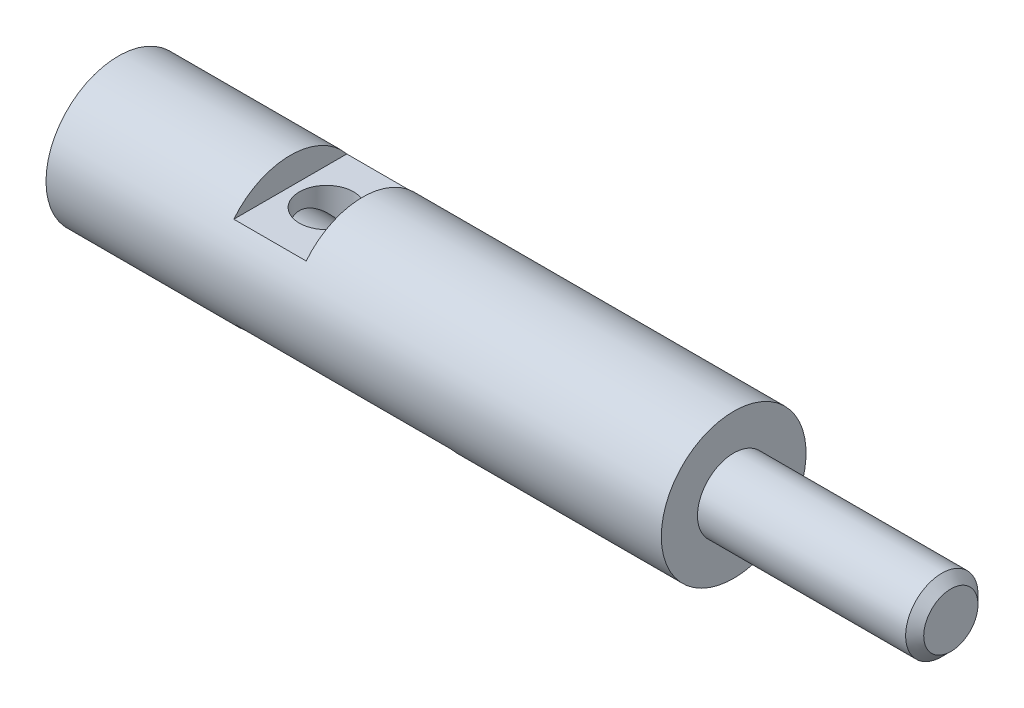
SolidWorks part; units mm, degrees
ref_plane "Front Plane" through (0, 0, 0) normal (0, 0, 1) x (1, 0, 0)
ref_plane "Top Plane" through (0, 0, 0) normal (0, 1, 0) x (1, 0, 0)
ref_plane "Right Plane" through (0, 0, 0) normal (1, 0, 0) x (0, 0, -1)
sketch "Эскиз1" plane through (0, 0, 0) normal (0, 0, 1) x (1, 0, 0)
  line L0 (0, 0) -> (27.7422, 0) construction
  line L1 (0, 0) -> (0, 4)
  line L2 (0, 4) -> (34, 4)
  line L3 (34, 4) -> (34, 2)
  line L4 (34, 2) -> (45.5, 2)
  line L5 (46, 1.5) -> (46, 0)
  line L6 (46, 0) -> (0, 0)
  line L7 (45.5, 2) -> (46, 1.5)
  point P7 (46, 2)
  dimension "D1" = 4
  dimension "D2" = 34
  dimension "D3" = 2
  dimension "D4" = 12
  dimension "D5" = 0.5
  dimension "D6" = 45
revolve "Повернуть1" add sketch "Эскиз1" angle 360 about L0
sketch "Эскиз3" plane through (0, 0, 0) normal (0, 0, 1) x (1, 0, 0)
  line L0 (9.5, -2.5) -> (21.5, -2.5)
  line L1 (9.5, -2.5) -> (9.5, -5.9267)
  line L2 (21.5, -2.5) -> (21.5, -5.9267)
  line L3 (9.5, -5.9267) -> (21.5, -5.9267)
  line L4 (0, -4) -> (34, -4) construction
  line L5 (0, 4) -> (0, -4) construction
  line L6 (9.5, 2.5) -> (13.5, 2.5)
  line L7 (9.5, 2.5) -> (9.5, 4.9583)
  line L8 (13.5, 2.5) -> (13.5, 4.9583)
  line L9 (9.5, 4.9583) -> (13.5, 4.9583)
  line L10 (34, 4) -> (0, 4) construction
  point P6 (9.5, 3.7291)
  dimension "D1" = 12
  dimension "D2" = 3.4267
  dimension "D3" = 1.5
  dimension "D4" = 9.5
  dimension "D5" = 4
  dimension "D6" = 2.4583
  dimension "D7" = 9.5
  dimension "D8" = 1.5
extrude "Вырез-Вытянуть1" cut sketch "Эскиз3" along normal through all and the other way through all
hole_wizard "Диаметр отверстия Ø3.2 (3.2)1" positions "Эскиз5" profile "Эскиз4" hole size "Ø3.2" standard "Ansi Metric"
sketch "Эскиз5" plane through (0, 0, 0) normal (-1, 0, 0) x (0, 0, 1)
  point P1 (0, 0)
sketch "Эскиз4" plane through (0, 0, 0) normal (0, 1, 0) x (0, 0, 1)
  line L0 (0, 0) -> (0, 14.9614)
  line L1 (0, 14.9614) -> (1.6, 14)
  line L2 (1.6, 14) -> (1.6, 0)
  line L5 (1.6, 0) -> (0, 0)
  line L10 (0, 14.9614) -> (-1.6, 14) construction
  line L11 (0, -6.35) -> (0, 107.95) construction
  dimension "Диаметр отверстия" = 3.2
  dimension "Глубина отверстия" = 14
  dimension "Угол заточки сверла" = 118
sketch "Эскиз6" plane through (0, 2.5, 0) normal (0, 1, 0) x (1, 0, 0)
  line L0 (11.5, 3.1225) -> (11.5, -3.1225) construction
  line L1 (13.5, 3.1225) -> (9.5, 3.1225) construction
  line L2 (9.5, -3.1225) -> (13.5, -3.1225) construction
  line L3 (9.5, 0) -> (13.5, 0) construction
  line L4 (9.5, -3.1225) -> (9.5, 3.1225) construction
  line L5 (13.5, -3.1225) -> (13.5, 3.1225) construction
  circle A0 centre (11.5, 0) radius 1.5
  dimension "D1" = 3
extrude "Вырез-Вытянуть2" cut sketch "Эскиз6" against normal up to surface (1.9432 mm away)
